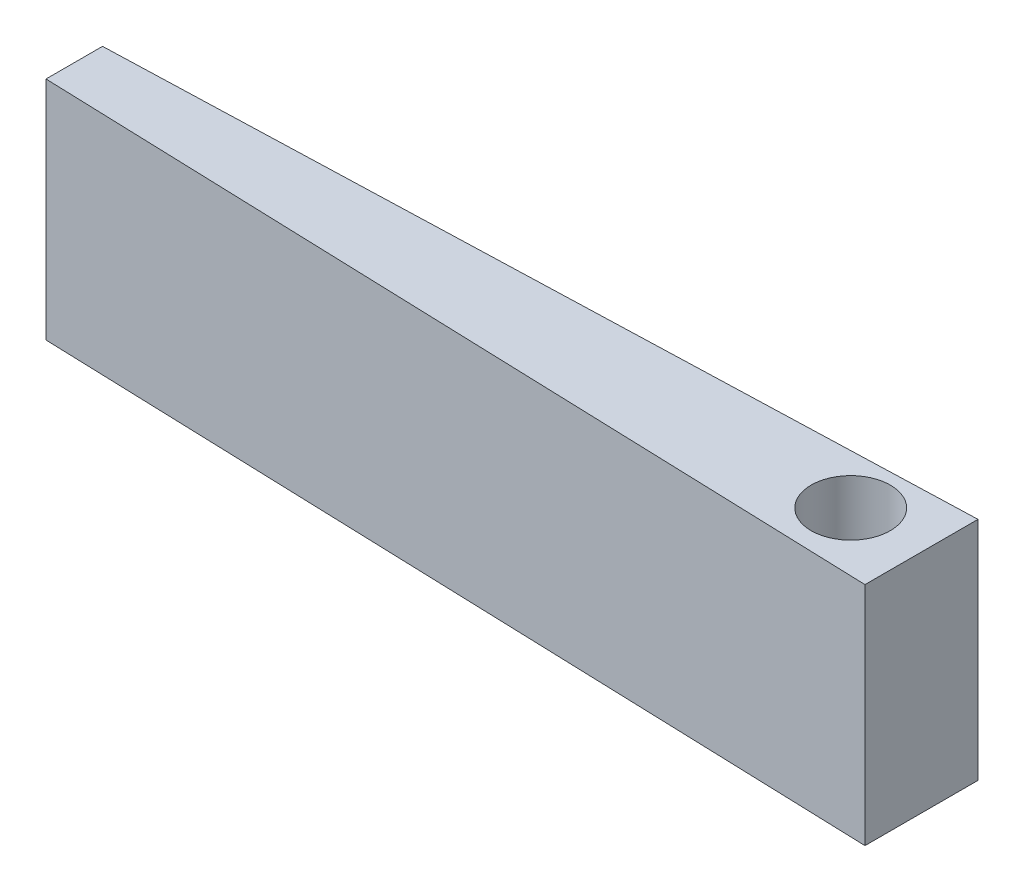
SolidWorks part; units mm, degrees
ref_plane "Front Plane" through (0, 0, 0) normal (0, 0, 1) x (1, 0, 0)
ref_plane "Top Plane" through (0, 0, 0) normal (0, 1, 0) x (1, 0, 0)
ref_plane "Right Plane" through (0, 0, 0) normal (1, 0, 0) x (0, 0, -1)
sketch "Sketch1" plane through (0, 0, 0) normal (0, 1, 0) x (1, 0, 0)
  line L0 (-46.9032, -0.4683) -> (-46.9032, -10.4683)
  line L1 (-46.9032, -0.4683) -> (103.0143, 4.505)
  line L2 (103.0143, 4.505) -> (103.0143, -15.495)
  line L3 (103.0143, -15.495) -> (-46.9032, -10.4683)
extrude "Boss-Extrude1" add sketch "Sketch1" along normal blind 40
sketch "Sketch2" plane through (0, 40, 0) normal (0, 1, 0) x (1, 0, 0)
  circle A0 centre (90, -5) radius 7
extrude "Cut-Extrude1" cut sketch "Sketch2" against normal blind 25
